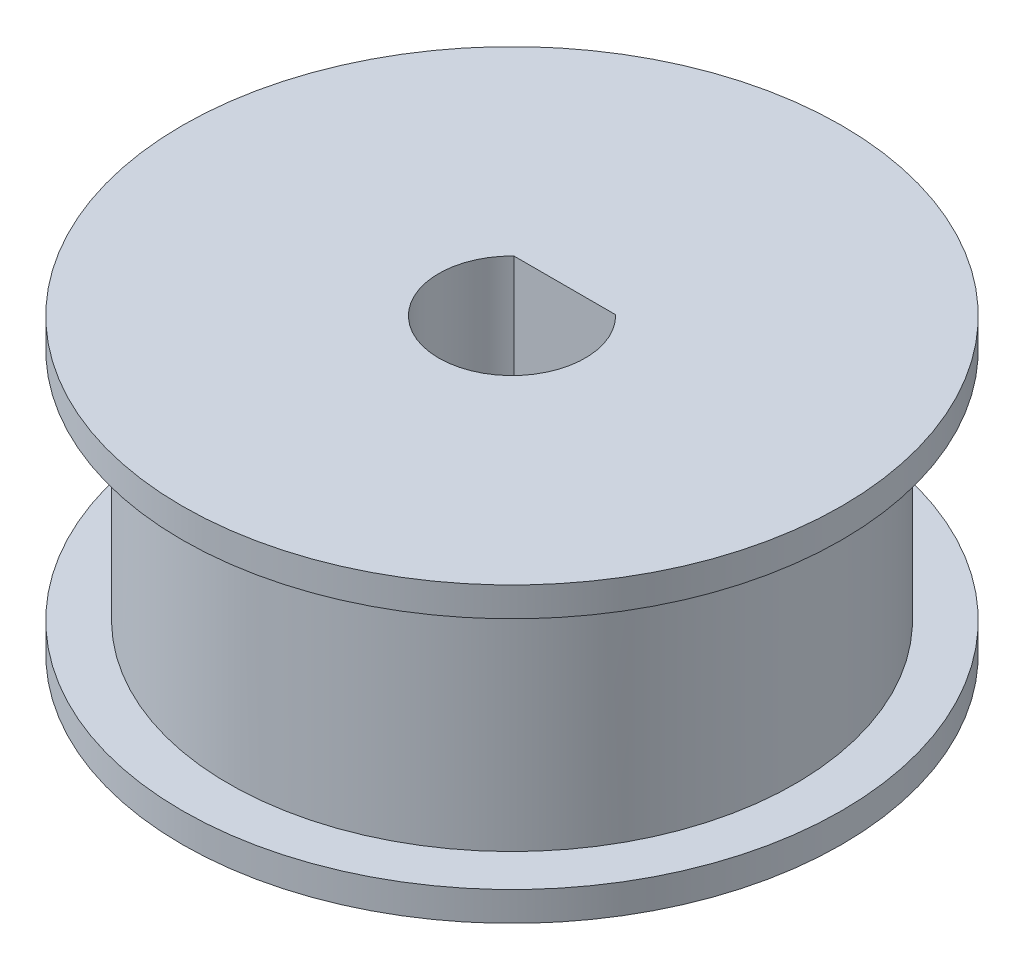
SolidWorks part; units mm, degrees
material "6061 合金"
ref_plane "前视基准面" through (0, 0, 0) normal (0, 0, 1) x (1, 0, 0)
ref_plane "上视基准面" through (0, 0, 0) normal (0, 1, 0) x (1, 0, 0)
ref_plane "右视基准面" through (0, 0, 0) normal (1, 0, 0) x (0, 0, -1)
sketch "草图1" plane through (0, 0, 0) normal (0, 1, 0) x (1, 0, 0)
  circle A0 centre (0, 0) radius 2.5
  circle A1 centre (0, 0) radius 19.325
  dimension "D1" = 5
  dimension "D2" = 38.65
extrude "凸台-拉伸1" add sketch "草图1" along normal blind 16
sketch "草图2" plane through (0, 16, 0) normal (0, 1, 0) x (1, 0, 0)
  circle A0 centre (0, 0) radius 22.5
  circle A1 centre (0, 0) radius 2.5
  dimension "D1" = 45
extrude "凸台-拉伸2" add sketch "草图2" along normal blind 2
sketch "草图3" plane through (0, 0, 0) normal (0, -1, 0) x (1, 0, 0)
  circle A0 centre (0, 0) radius 2.5
  circle A1 centre (0, 0) radius 22.5
  dimension "D1" = 45
extrude "凸台-拉伸3" add sketch "草图3" along normal blind 2
sketch "草图4" plane through (0, 18, 0) normal (0, 1, 0) x (1, 0, 0)
  line L0 (-3.4699, 3.6) -> (3.4699, 3.6)
  arc A0 (-3.4699, 3.6) -> (3.4699, 3.6) centre (0, 0) ccw
  dimension "D1" = 10
  dimension "D2" = 3.6
extrude "切除-拉伸1" cut sketch "草图4" against normal up to next
